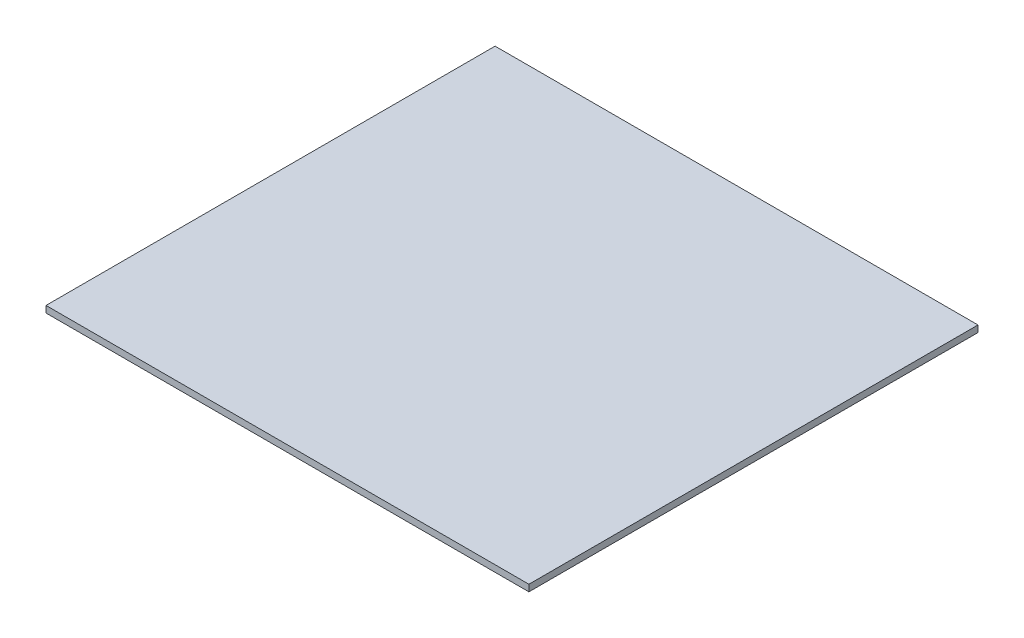
SolidWorks part; units mm, degrees
material "Polyethylene Cross-Linked"
ref_plane "Front Plane" through (0, 0, 0) normal (0, 0, 1) x (1, 0, 0)
ref_plane "Top Plane" through (0, 0, 0) normal (0, 1, 0) x (1, 0, 0)
ref_plane "Right Plane" through (0, 0, 0) normal (1, 0, 0) x (0, 0, -1)
sketch "Sketch1" plane through (0, 0, 0) normal (0, 1, 0) x (1, 0, 0)
  line L1 (0, 0) -> (232.156, 0)
  line L3 (0, 215.9) -> (232.156, 215.9)
  line L8 (232.156, 215.9) -> (232.156, 0)
  line L41 (0, 0) -> (0, 215.9)
extrude "Boss-Extrude1" add sketch "Sketch1" along normal blind 3.175
ref_plane "Plane1" through (232.156, 3.175, -215.9) normal (-1, 0, 0) x (0, 0, 1)
